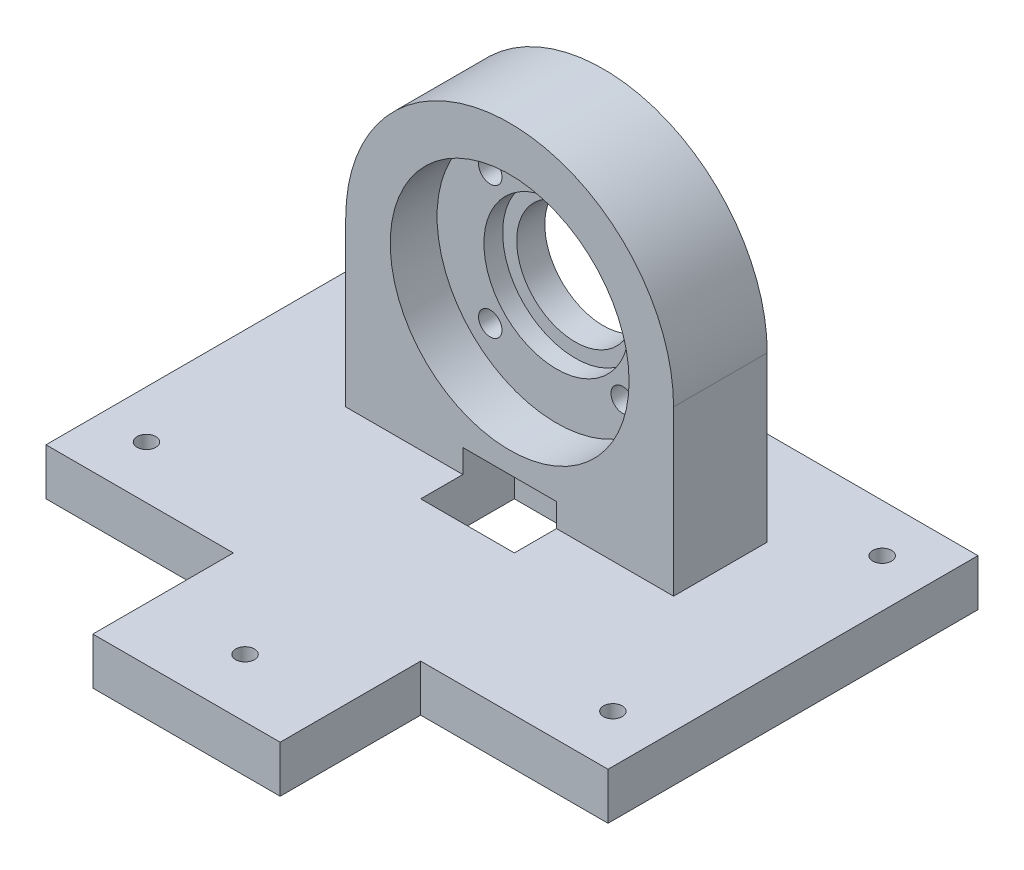
SolidWorks part; units mm, degrees
ref_plane "Front Plane" through (0, 0, 0) normal (0, 0, 1) x (1, 0, 0)
ref_plane "Top Plane" through (0, 0, 0) normal (0, 1, 0) x (1, 0, 0)
ref_plane "Right Plane" through (0, 0, 0) normal (1, 0, 0) x (0, 0, -1)
sketch "Sketch1" plane through (0, 0, 0) normal (0, 1, 0) x (1, 0, 0)
  line L0 (0, -114.1661) -> (0, 132.8372) construction
  line L1 (135.7044, 0) -> (-145.1402, 0) construction
  line L2 (-35, -40) -> (-20, -40)
  line L3 (-35, 19) -> (35, 19) construction
  line L4 (-35, 19) -> (-35, -40) construction
  line L5 (-20, -70) -> (20, -70)
  line L6 (35, 19) -> (35, -40) construction
  line L7 (-20, -40) -> (-20, -70)
  line L8 (35, -40) -> (20, -40)
  line L9 (20, -40) -> (20, -70)
  line L10 (-35, -40) -> (-60, -40)
  line L11 (-60, -40) -> (-60, 39)
  line L12 (-60, 39) -> (60, 39)
  line L13 (60, 39) -> (60, -40)
  line L14 (60, -40) -> (35, -40)
  circle A0 centre (0, 0) radius 57.5 construction
  circle A1 centre (0, 0) radius 2.5 construction
  circle A2 centre (0, 57.5) radius 2 construction
  circle A3 centre (49.7965, 28.75) radius 2
  circle A4 centre (49.7965, -28.75) radius 2
  circle A5 centre (0, -57.5) radius 2
  circle A6 centre (-49.7965, -28.75) radius 2
  circle A7 centre (-49.7965, 28.75) radius 2
  point P22 (0, 0)
  dimension "D1" = 115
  dimension "D2" = 4
  dimension "D3" = 5
  dimension "D4" = 6
  dimension "D5" = 70
  dimension "D6" = 19
  dimension "D7" = 35
  dimension "D8" = 25
  dimension "D9" = 30
  dimension "D10" = 15
  dimension "D11" = 30
  dimension "D12" = 15
  dimension "D13" = 25
  dimension "D14" = 20
extrude "Boss-Extrude1" add sketch "Sketch1" along normal blind 10
sketch "Sketch2" plane through (0, 10, 0) normal (0, 1, 0) x (1, 0, 0)
  line L1 (-35, 19) -> (35, 19)
  line L2 (-35, 19) -> (-35, -1)
  line L3 (-35, -1) -> (35, -1)
  line L4 (35, -1) -> (35, 19)
  dimension "D1" = 70
  dimension "D2" = 20
  dimension "D3" = 19
extrude "Boss-Extrude2" add sketch "Sketch2" along normal blind 70
sketch "Sketch3" plane through (0, 0, -19) normal (0, 0, -1) x (-1, 0, 0)
  line L0 (-35, 80) -> (35, 80) construction
  line L1 (35, 80) -> (35, 10) construction
  line L2 (-35, 80) -> (-35, 10) construction
  line L3 (35, 80) -> (35, 45)
  line L4 (-35, 80) -> (-35, 45)
  line L5 (-35, 80) -> (35, 80)
  arc A0 (35, 45) -> (-35, 45) centre (0, 45) ccw
  line M2 (35, 10) -> (35, 80)
  line M3 (35, 80) -> (-35, 80)
  line M4 (-35, 80) -> (-35, 10)
  dimension "D1" = 70
extrude "Cut-Extrude1" cut sketch "Sketch3" against normal blind 20 contours A0 L5 M4 | A0 M2 M3
sketch "Sketch4" plane through (0, 0, 1) normal (0, 0, 1) x (1, 0, 0)
  circle A0 centre (0, 45) radius 25.5
  dimension "D1" = 51
extrude "Cut-Extrude2" cut sketch "Sketch4" against normal blind 10
sketch "Sketch5" plane through (0, 0, -9) normal (0, 0, 1) x (1, 0, 0)
  circle A0 centre (0, 45) radius 15.5
  dimension "D1" = 31
extrude "Cut-Extrude3" cut sketch "Sketch5" against normal blind 4
sketch "Sketch6" plane through (0, 0, -9) normal (0, 0, 1) x (1, 0, 0)
  line L0 (0, 45) -> (0, 84.8446) construction
  line L1 (0, 45) -> (33.4312, 78.4312) construction
  circle A0 centre (0, 45) radius 20 construction
  circle A2 centre (14.1421, 59.1421) radius 2.5
  circle A3 centre (14.1421, 30.8579) radius 2.5
  circle A4 centre (-14.1421, 30.8579) radius 2.5
  circle A5 centre (-14.1421, 59.1421) radius 2.5
  point P17 (0, 45)
  dimension "D1" = 40
  dimension "D3" = 5
  dimension "D2" = 45
  dimension "D4" = 4
extrude "Cut-Extrude4" cut sketch "Sketch6" against normal up to surface (10 mm away) up to face at (0, 36.25, -19)
sketch "Sketch7" plane through (0, 0, -13) normal (0, 0, 1) x (1, 0, 0)
  circle A0 centre (0, 45) radius 12.5
  dimension "D1" = 25
extrude "Cut-Extrude5" cut sketch "Sketch7" against normal up to surface (6 mm away) up to face at (16.6421, 30.8579, -19)
sketch "Sketch8" plane through (0, 0, 0) normal (0, -1, 0) x (1, 0, 0)
  line L0 (0, 70) -> (0, 0) construction
  line L1 (-20, 70) -> (20, 70) construction
  line L3 (-10, -10) -> (10, -10)
  line L4 (-10, -10) -> (-10, 10)
  line L5 (-10, 10) -> (10, 10)
  line L6 (10, -10) -> (10, 10)
  line L7 (-10, -10) -> (10, 10) construction
  line L8 (-10, 10) -> (10, -10) construction
  dimension "D1" = 70
  dimension "D2" = 20
  dimension "D3" = 20
extrude "Cut-Extrude6" cut sketch "Sketch8" against normal blind 15
